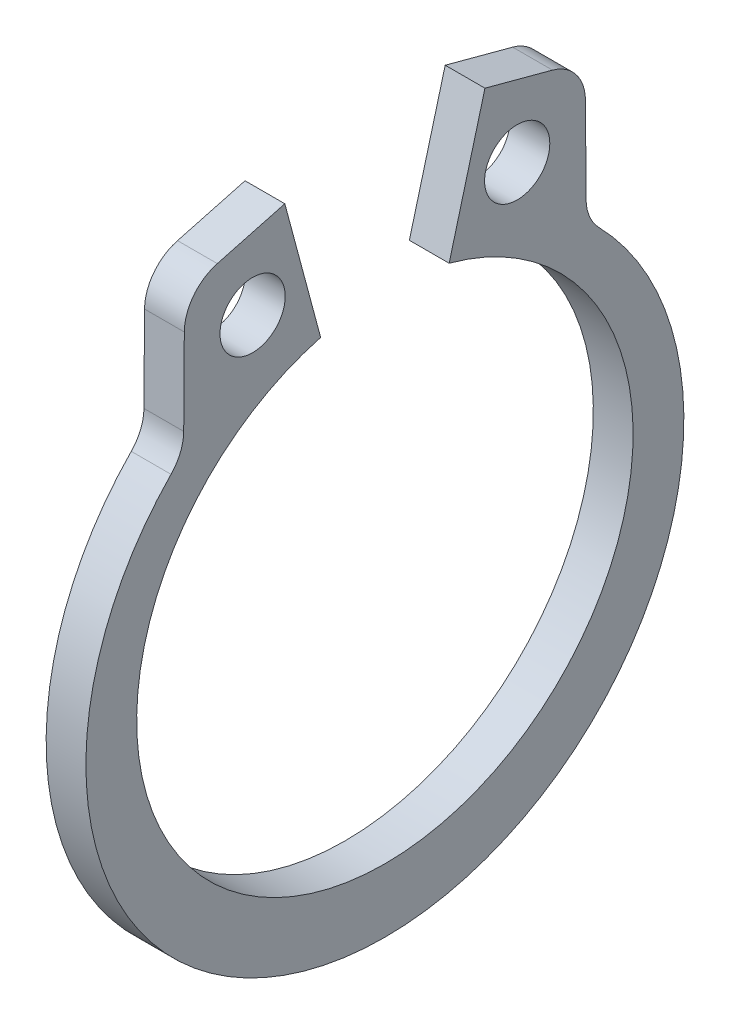
SolidWorks part; units mm, degrees
material "Cast Carbon Steel"
ref_plane "Front" through (0, 0, 0) normal (0, 0, 1) x (1, 0, 0)
ref_plane "Top" through (0, 0, 0) normal (0, 1, 0) x (1, 0, 0)
ref_plane "Right" through (0, 0, 0) normal (1, 0, 0) x (0, 0, -1)
sketch "Sketch1" plane through (0, 0, 0) normal (1, 0, 0) x (0, 0, -1)
  line L0 (0, 0) -> (0, 3.9624) construction
  line L1 (-1.0255, 3.8274) -> (-1.5975, 5.9619)
  line L2 (1.5975, 5.9619) -> (3.1984, 5.5329)
  line L3 (3.1984, 5.5329) -> (3.2135, 3.3232)
  line L4 (1.0255, 3.8274) -> (1.5975, 5.9619)
  line L5 (-1.5975, 5.9619) -> (-3.1984, 5.5329)
  line L6 (-3.1984, 5.5329) -> (-3.2135, 3.3232)
  line L7 (-3.2135, 3.3232) -> (-2.7544, 2.8484) construction
  line L8 (3.2135, 3.3232) -> (2.7544, 2.8484) construction
  line L9 (0, -3.9624) -> (0, -4.9784) construction
  line L10 (-3.1984, 5.5329) -> (-1.0255, 3.8274) construction
  line L11 (0, 3.9624) -> (0, 6.1722) construction
  line L12 (-3.9624, 0) -> (3.9624, 0) construction
  circle A0 centre (0, 0) radius 3.9624 construction
  arc A1 (-1.0255, 3.8274) -> (1.0255, 3.8274) centre (0, 0) ccw
  circle A3 centre (0, 0) radius 6.858 construction
  circle A4 centre (-2.112, 4.6802) radius 0.5207
  circle A5 centre (2.112, 4.6802) radius 0.5207
  arc A6 (-3.2135, 3.3232) -> (3.2135, 3.3232) centre (0, -0.2056) ccw
  point P0 (0, -4.9784)
  dimension "A" = 7.9248
  dimension "D2" = 1.6573
  dimension "L" = 13.716
  dimension "Hole" = 1.0414
  dimension "Smin" = 0.6604
  dimension "Smax" = 1.016
  dimension "H" = 2.2098
  dimension "Angle" = 15
extrude "Extrude1" add sketch "Sketch1" along normal mid plane 0.635
fillet "Fillet1" radius 0.7112 4 edges at (0, 3.3232, 3.2135) (0, 3.3232, -3.2135) (0, 5.5329, 3.1984) (0, 5.5329, -3.1984)
sketch "Sketch2" plane through (0, 0, 0) normal (0, 0, 1) x (1, 0, 0)
  line L0 (-3.5433, 0) -> (9.1567, 0)
  line L1 (9.1567, 0) -> (9.1567, -3.9624)
  line L2 (-0.3683, -3.9624) -> (-3.2639, -3.9624)
  line L3 (9.1567, -3.9624) -> (0.3683, -3.9624)
  line L4 (0.3683, -3.9624) -> (0.3683, -3.683)
  line L5 (0.3683, -3.683) -> (-0.3683, -3.683)
  line L6 (-0.3683, -3.683) -> (-0.3683, -3.9624)
  line L7 (-0.3683, -3.9624) -> (-3.5433, -3.9624) construction
  line L8 (-3.5433, -3.9624) -> (-3.5433, 0) construction
  line L9 (9.1567, 0) -> (76.391, 0) construction
  line L10 (-3.2639, -3.9624) -> (-3.5433, -3.683)
  line L11 (-3.5433, -3.683) -> (-3.5433, 0)
  point P10 (0, -3.683)
  dimension "D1" = 45
  dimension "Dg" = 7.366
  dimension "Ds" = 7.9248
  dimension "W" = 0.7366
  dimension "D2" = 12.7
  dimension "D3" = 3.175
revolve "Revolve1" [suppressed] add sketch "Sketch2" angle 360 about L9
delete or keep bodies "Body-Delete1" [suppressed] type delete bodies bodies 122
equation "\"D2@Sketch2\" = \"D1@Extrude1\"*20"
equation "\"D3@Sketch2\" = \"D2@Sketch2\"/4"
equation "\"D2@Sketch1\" = \"H@Sketch1\"*.75"
